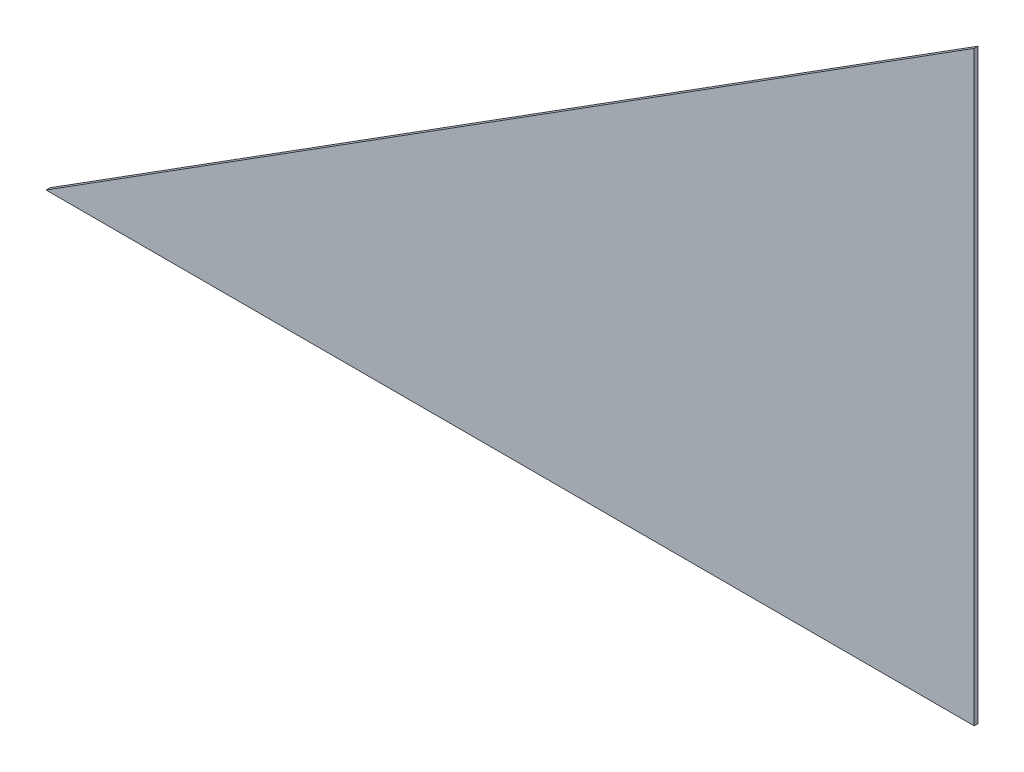
SolidWorks part; units mm, degrees
ref_plane "Front Plane" through (0, 0, 0) normal (0, 0, 1) x (1, 0, 0)
ref_plane "Top Plane" through (0, 0, 0) normal (0, 1, 0) x (1, 0, 0)
ref_plane "Right Plane" through (0, 0, 0) normal (1, 0, 0) x (0, 0, -1)
sketch "Sketch1" plane through (0, 0, 1121.2546) normal (0, 0, -1) x (-1, 0, 0)
  line L0 (86.1675, 1821.5171) -> (-523.4325, 1821.5171)
  line L1 (39.9292, 1821.5171) -> (-1204.6708, 1821.5171) construction
  line L2 (-523.4325, 1821.5171) -> (-523.4325, 2206.8544)
  line L3 (85.649, 1821.5169) -> (-1158.9508, 2608.9171) construction
  line L4 (-523.4325, 2206.8544) -> (86.1675, 1821.5171)
  dimension "D1" = 609.6
extrude "Boss-Extrude1" add sketch "Sketch1" along normal blind 2.54
